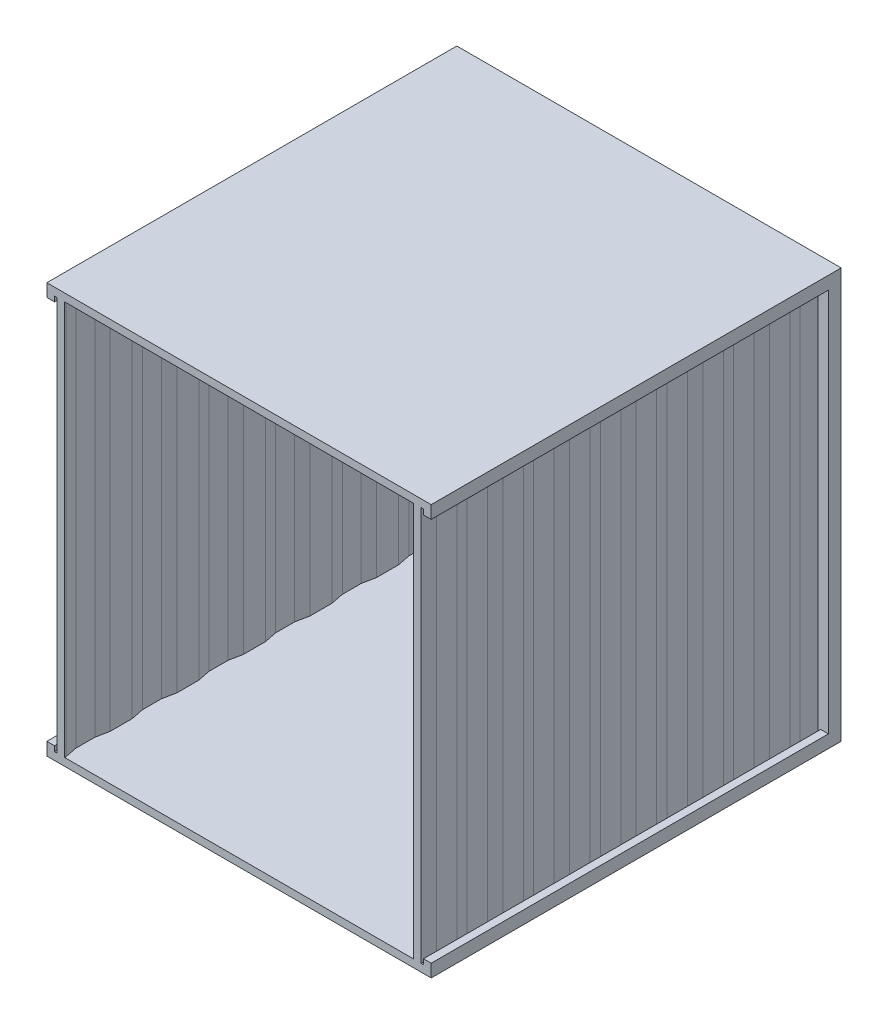
SolidWorks part; units mm, degrees
ref_plane "Front Plane" through (0, 0, 0) normal (0, 0, 1) x (1, 0, 0)
ref_plane "Top Plane" through (0, 0, 0) normal (0, 1, 0) x (1, 0, 0)
ref_plane "Right Plane" through (0, 0, 0) normal (1, 0, 0) x (0, 0, -1)
sketch "Sketch1" plane through (0, 0, 0) normal (0, 0, 1) x (1, 0, 0)
  line L1 (-75, 80) -> (75, 80)
  line L2 (-75, 80) -> (-75, -80)
  line L3 (-75, -80) -> (75, -80)
  line L4 (75, 80) -> (75, -80)
  line L5 (-75, 80) -> (75, -80) construction
  line L6 (-75, -80) -> (75, 80) construction
  line L7 (-65, 70) -> (65, 70)
  line L8 (-65, 70) -> (-65, -70)
  line L9 (-65, -70) -> (65, -70)
  line L10 (65, 70) -> (65, -70)
  line L11 (-65, 70) -> (65, -70) construction
  line L12 (-65, -70) -> (65, 70) construction
  point P0 (0, 0)
  point P6 (0, 0)
  dimension "D1" = 150
  dimension "D2" = 160
  dimension "D3" = 10
  dimension "D4" = 10
  dimension "D5" = 10
  dimension "D6" = 10
extrude "Boss-Extrude1" add sketch "Sketch1" along normal blind 5
sketch "Sketch2" plane through (0, 0, 5) normal (0, 0, 1) x (1, 0, 0)
  line L0 (-75, 80) -> (-70, 80)
  line L1 (75, 80) -> (-75, 80) construction
  line L2 (-70, 80) -> (-70, 77)
  line L7 (-72, 75) -> (-75, 75)
  line L8 (-75, 80) -> (-75, -80) construction
  line L9 (-75, 75) -> (-75, 80)
  line L10 (-70, 77) -> (-72, 77)
  line L11 (-72, 77) -> (-72, 75)
  line L12 (0, 80) -> (0, -80) construction
  line L13 (-75, -80) -> (75, -80) construction
  line L14 (72, 75) -> (75, 75)
  line L15 (72, 77) -> (72, 75)
  line L16 (75, 75) -> (75, 80)
  line L17 (70, 77) -> (72, 77)
  line L18 (70, 80) -> (70, 77)
  line L19 (75, 80) -> (70, 80)
  line L20 (-75, 0) -> (75, 0) construction
  line L21 (75, -80) -> (75, 80) construction
  line L22 (75, -75) -> (75, -80)
  line L23 (72, -75) -> (75, -75)
  line L24 (72, -77) -> (72, -75)
  line L25 (70, -77) -> (72, -77)
  line L26 (75, -80) -> (70, -80)
  line L27 (70, -80) -> (70, -77)
  line L28 (-70, -80) -> (-70, -77)
  line L29 (-72, -75) -> (-75, -75)
  line L30 (-72, -77) -> (-72, -75)
  line L31 (-70, -77) -> (-72, -77)
  line L32 (-75, -80) -> (-70, -80)
  line L33 (-75, -75) -> (-75, -80)
  dimension "D1" = 5
  dimension "D2" = 5
  dimension "D3" = 3
  dimension "D4" = 3
extrude "Boss-Extrude2" add sketch "Sketch2" along normal blind 155
sketch "Sketch3" plane through (0, -77, 0) normal (0, 1, 0) x (1, 0, 0)
  line L0 (-71, -5) -> (-71, -160) construction
  line L1 (-70, -5) -> (-72, -5) construction
  line L2 (-70, -160) -> (-72, -160) construction
  line L3 (-71, -160) -> (-72, -155)
  line L4 (-72, -160) -> (-72, -5) construction
  line L5 (-72, -155) -> (-72, -147)
  line L6 (-72, -147) -> (-71, -142)
  line L7 (-71, -142) -> (-71, -134)
  line L8 (-71, -134) -> (-72, -129)
  line L9 (-72, -129) -> (-72, -121)
  line L10 (-72, -121) -> (-71, -116)
  line L11 (-71, -116) -> (-71, -108)
  line L12 (-71, -108) -> (-72, -103)
  line L13 (-72, -103) -> (-72, -95)
  line L14 (-72, -95) -> (-71, -90)
  line L15 (-71, -90) -> (-71, -82)
  line L16 (-71, -82) -> (-72, -77)
  line L17 (-72, -77) -> (-72, -69)
  line L18 (-72, -69) -> (-71, -64)
  line L19 (-71, -64) -> (-71, -56)
  line L20 (-71, -56) -> (-72, -51)
  line L21 (-72, -51) -> (-72, -43)
  line L22 (-72, -43) -> (-71, -38)
  line L23 (-71, -38) -> (-71, -30)
  line L24 (-72, -17) -> (-71, -12)
  line L25 (-68.0583, -159.4117) -> (-69, -154.7029)
  line L26 (-71, -30) -> (-72, -25)
  line L27 (-72, -25) -> (-72, -17)
  line L28 (-71, -12) -> (-71, -5)
  line L29 (-71, -5) -> (-68, -5)
  line L30 (-69, -154.7029) -> (-69, -147.2971)
  line L31 (-69, -147.2971) -> (-68, -142.2971)
  line L32 (-68, -142.2971) -> (-68, -133.7029)
  line L33 (-68, -133.7029) -> (-69, -128.7029)
  line L34 (-69, -128.7029) -> (-69, -121.2971)
  line L35 (-69, -121.2971) -> (-68, -116.2971)
  line L36 (-68, -116.2971) -> (-68, -107.7029)
  line L37 (-68, -107.7029) -> (-69, -102.7029)
  line L38 (-69, -102.7029) -> (-69, -95.2971)
  line L39 (-69, -95.2971) -> (-68, -90.2971)
  line L40 (-68, -90.2971) -> (-68, -81.7029)
  line L41 (-68, -81.7029) -> (-69, -76.7029)
  line L42 (-69, -76.7029) -> (-69, -69.2971)
  line L43 (-69, -69.2971) -> (-68, -64.2971)
  line L44 (-68, -64.2971) -> (-68, -55.7029)
  line L45 (-68, -55.7029) -> (-69, -50.7029)
  line L46 (-69, -50.7029) -> (-69, -43.2971)
  line L47 (-69, -43.2971) -> (-68, -38.2971)
  line L48 (-68, -38.2971) -> (-68, -29.7029)
  line L49 (-68, -29.7029) -> (-69, -24.7029)
  line L50 (-69, -24.7029) -> (-69, -17.2971)
  line L51 (-69, -17.2971) -> (-68, -12.2971)
  line L52 (-68, -12.2971) -> (-68, -5)
  line L53 (-68.0583, -159.4117) -> (-68.0583, -160)
  line L54 (-68.0583, -160) -> (-71, -160)
  dimension "D1" = 5
  dimension "D2" = 8
  dimension "D3" = 5
  dimension "D4" = 8
  dimension "D5" = 5
  dimension "D6" = 8
  dimension "D7" = 5
  dimension "D8" = 8
  dimension "D9" = 5
  dimension "D10" = 8
  dimension "D11" = 5
  dimension "D12" = 8
  dimension "D13" = 8
  dimension "D14" = 5
  dimension "D15" = 8
  dimension "D16" = 5
  dimension "D17" = 8
  dimension "D18" = 5
  dimension "D19" = 8
  dimension "D20" = 5
  dimension "D21" = 8
  dimension "D22" = 5
  dimension "D24" = 3
extrude "Boss-Extrude3" add sketch "Sketch3" along normal up to surface (154 mm away) up to face at (-71, 77, 82.5)
mirror "Mirror1" about plane through (0, 0, 0) normal (1, 0, 0) of "Boss-Extrude3"
sketch "Sketch4" plane through (-70, 0, 0) normal (1, 0, 0) x (0, 0, -1)
  line L4 (-5, 77) -> (-5, 80)
  line L5 (-5, 80) -> (-160, 80)
  line L6 (-160, 80) -> (-160, 77)
  line L7 (-160, 77) -> (-5, 77)
  line L8 (-5, 77) -> (-5, 80)
  line L9 (-5, 80) -> (-160, 80)
  line L10 (-160, 80) -> (-160, 77)
  line L12 (-160, 77) -> (-5, 77)
  dimension "D1" = 0
extrude "Boss-Extrude4" add sketch "Sketch4" along normal up to surface (140 mm away) up to face at (70, 78.5, 82.5)
sketch "Sketch5" plane through (-70, 0, 0) normal (1, 0, 0) x (0, 0, -1)
  line L4 (-5, -80) -> (-5, -77)
  line L5 (-5, -77) -> (-160, -77)
  line L6 (-160, -77) -> (-160, -80)
  line L7 (-160, -80) -> (-5, -80)
  line L8 (-5, -80) -> (-5, -77)
  line L10 (-160, -77) -> (-160, -80)
  line L11 (-160, -80) -> (-5, -80)
  line L12 (-5, -77) -> (-160, -77)
  dimension "D1" = 0
extrude "Boss-Extrude5" add sketch "Sketch5" along normal up to surface (140 mm away) up to face at (70, -78.5, 82.5)
